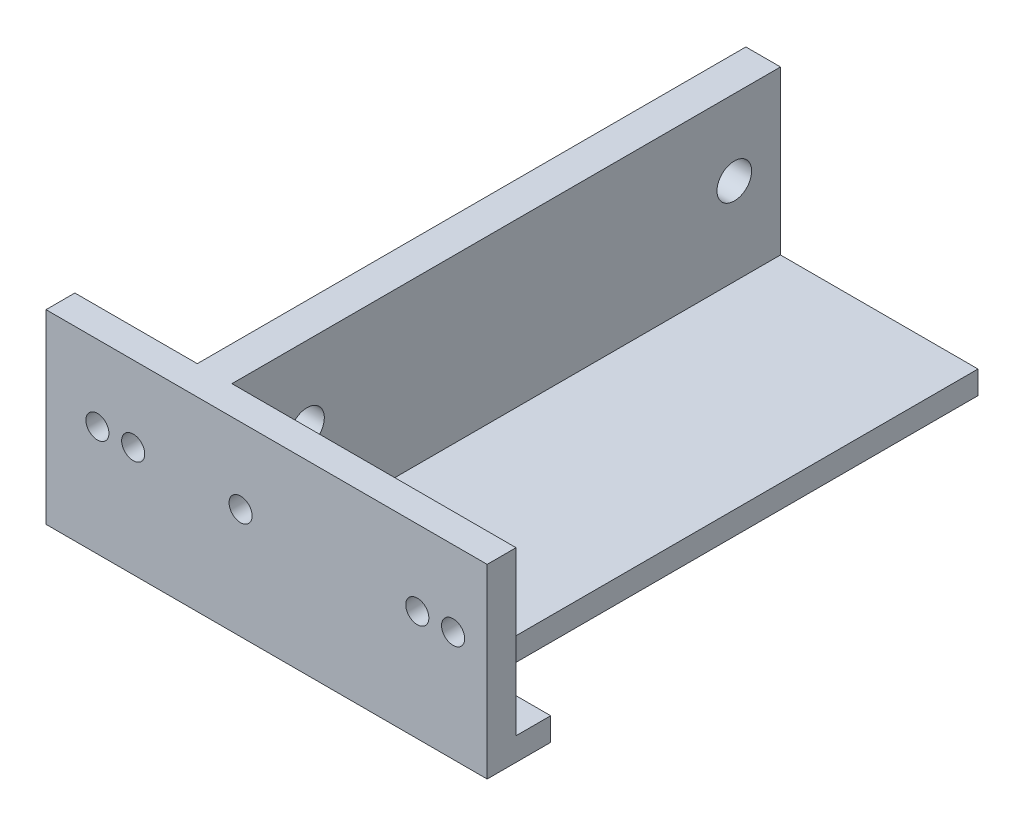
SolidWorks part; units mm, degrees
ref_plane "Front Plane" through (0, 0, 0) normal (0, 0, 1) x (1, 0, 0)
ref_plane "Top Plane" through (0, 0, 0) normal (0, 1, 0) x (1, 0, 0)
ref_plane "Right Plane" through (0, 0, 0) normal (1, 0, 0) x (0, 0, -1)
sketch "Sketch1" plane through (0, 0, 0) normal (1, 0, 0) x (0, 0, -1)
  line L1 (0, 0) -> (50, 0)
  line L2 (0, 0) -> (0, 16.1)
  line L3 (0, 16.1) -> (50, 16.1)
  line L4 (50, 0) -> (50, 16.1)
  dimension "D1" = 50
  dimension "D2" = 16.1
extrude "Boss-Extrude1" add sketch "Sketch1" along normal blind 3
sketch "Sketch3" plane through (3, 0, 0) normal (1, 0, 0) x (0, 0, -1)
  line L0 (0, 9.55) -> (50, 9.55) construction
  line L2 (50, 0) -> (50, 16.1) construction
  line L3 (50, 16.1) -> (0, 16.1) construction
  circle A0 centre (46, 9.55) radius 1.5
  circle A1 centre (9, 9.55) radius 1.5
  dimension "D1" = 37
  dimension "D2" = 4
  dimension "D3" = 3
  dimension "D4" = 6.55
extrude "Cut-Extrude1" cut sketch "Sketch3" against normal through all
sketch "Sketch4" plane through (3, 0, 0) normal (1, 0, 0) x (0, 0, -1)
  line L0 (50, 16.1) -> (0, 16.1) construction
  line L1 (0, 0) -> (2.5, 0)
  line L2 (0, 0) -> (0, 16.1)
  line L3 (0, 16.1) -> (2.5, 16.1)
  line L4 (2.5, 0) -> (2.5, 16.1)
  dimension "D1" = 2.5
extrude "Boss-Extrude2" add sketch "Sketch4" along normal blind 35.4 and the other way blind 13.6
sketch "Sketch6" plane through (0, 0, -2.5) normal (0, 0, -1) x (-1, 0, 0)
  line L0 (10.6, 9.55) -> (-38.4, 9.55) construction
  line L1 (-3, 16.1) -> (-3, 0) construction
  line L2 (10.6, 0) -> (10.6, 16.1) construction
  line L3 (-38.4, 16.1) -> (-3, 16.1) construction
  line L4 (-38.4, 0) -> (-38.4, 16.1) construction
  circle A0 centre (6.15, 9.55) radius 1
  circle A1 centre (3.05, 9.55) radius 1
  circle A2 centre (-0.05, 9.55) radius 1 construction
  circle A3 centre (-3.15, 9.55) radius 1 construction
  circle A4 centre (-6.25, 9.55) radius 1
  circle A5 centre (-21.55, 9.55) radius 1
  circle A6 centre (-24.65, 9.55) radius 1
  circle A7 centre (-27.75, 9.55) radius 1 construction
  circle A8 centre (-30.85, 9.55) radius 1 construction
  circle A9 centre (-33.95, 9.55) radius 1 construction
  dimension "D1" = 2
  dimension "D2" = 18.55
  dimension "D4" = 15.3
  dimension "D6" = 6.55
  dimension "D3" = 5
  dimension "D5" = 5
extrude "Cut-Extrude2" cut sketch "Sketch6" against normal blind 45
sketch "Sketch10" plane through (0, 0, -2.5) normal (0, 0, -1) x (-1, 0, 0)
  line L0 (10.6, 0) -> (10.6, 16.1) construction
  line L1 (-38.4, 0) -> (10.6, 0)
  line L2 (-38.4, 0) -> (-38.4, 2)
  line L3 (-38.4, 2) -> (10.6, 2)
  line L4 (10.6, 0) -> (10.6, 2)
  dimension "D1" = 2
extrude "Boss-Extrude4" add sketch "Sketch10" along normal up to surface (47.5 mm away) up to face at (1.5, 8.05, -50)
sketch "Sketch13" plane through (0, 2, 0) normal (0, 1, 0) x (1, 0, 0)
  line L0 (20.1, 5.5) -> (20.1, 50)
  line L1 (38.4, 0) -> (27.6, 0)
  line L2 (27.6, 0) -> (27.6, 5.5)
  line L3 (20.1, 50) -> (38.4, 50)
  line L4 (38.4, 50) -> (38.4, 0)
  line L6 (27.6, 5.5) -> (20.1, 5.5)
  line L7 (3, 50) -> (3, 2.5) construction
  line L8 (3, 2.5) -> (38.4, 2.5) construction
  line L9 (38.4, 0) -> (-10.6, 0) construction
  dimension "D1" = 3
  dimension "D2" = 17.1
  dimension "D3" = 7.5
extrude "Cut-Extrude5" cut sketch "Sketch13" against normal through all both and the other way through all
fillet "Fillet1" [suppressed] radius 10
sketch "Sketch8" plane through (2.5, 0, 0) normal (1, 0, 0) x (0, 0, -1)
  line L0 (2.5, 0) -> (2.5, 15.1) construction
  line L1 (2.5, 2) -> (50, 2)
  line L2 (2.5, 2) -> (2.5, 0)
  line L3 (2.5, 0) -> (50, 0)
  line L4 (50, 2) -> (50, 0)
  dimension "D1" = 2
extrude "Boss-Extrude3" [suppressed] add sketch "Sketch8" along normal up to surface (50 mm away)
sketch "Sketch9" [suppressed] plane through (0, 2, 0) normal (0, 1, 0) x (1, 0, 0)
  line L0 (45.2405, 2.5) -> (2.5, 43.1034)
  line L1 (52.5, 2.5) -> (2.5, 2.5) construction
  line L2 (2.5, 50) -> (2.5, 2.5) construction
  line L3 (52.5, 2.5) -> (2.5, 50)
  line L4 (17.5, 2.5) -> (2.5, 16.75)
  line L5 (2.5, 43.1034) -> (2.5, 23.6466)
  line L6 (2.5, 23.6466) -> (24.7595, 2.5)
  line L7 (24.7595, 2.5) -> (45.2405, 2.5)
  line L8 (17.5, 2.5) -> (2.5, 2.5)
  line L9 (2.5, 2.5) -> (2.5, 16.75)
  line L10 (52.5, 2.5) -> (52.5, 50)
  line L11 (52.5, 2.5) -> (52.5, 50) construction
  line L12 (52.5, 50) -> (2.5, 50) construction
  line L13 (52.5, 50) -> (2.5, 50)
  dimension "D1" = 5
  dimension "D2" = 5
  dimension "D3" = 15
extrude "Cut-Extrude3" [suppressed] cut sketch "Sketch9" against normal through all
